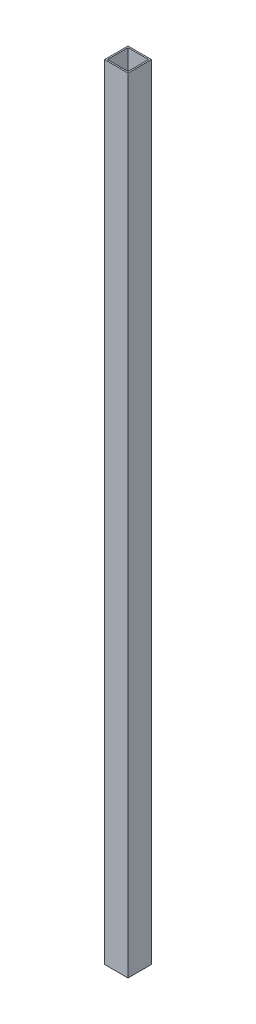
SolidWorks part; units mm, degrees
ref_plane "Front Plane" through (0, 0, 0) normal (0, 0, 1) x (1, 0, 0)
ref_plane "Top Plane" through (0, 0, 0) normal (0, 1, 0) x (1, 0, 0)
ref_plane "Right Plane" through (0, 0, 0) normal (1, 0, 0) x (0, 0, -1)
sketch "Sketch1" plane through (0, 0, 0) normal (0, 1, 0) x (1, 0, 0)
  line L1 (-14.5551, 17.2663) -> (10.8449, 17.2663)
  line L2 (-14.5551, 17.2663) -> (-14.5551, -8.1337)
  line L3 (-14.5551, -8.1337) -> (10.8449, -8.1337)
  line L4 (10.8449, 17.2663) -> (10.8449, -8.1337)
  line L5 (-13.0311, 15.7423) -> (9.3209, 15.7423)
  line L6 (-13.0311, 15.7423) -> (-13.0311, -6.6097)
  line L7 (-13.0311, -6.6097) -> (9.3209, -6.6097)
  line L8 (9.3209, 15.7423) -> (9.3209, -6.6097)
  point P8 (-1.8551, 17.2663)
  point P9 (-14.5551, 4.5663)
  dimension "D1" = 25.4
  dimension "D2" = 25.4
  dimension "D3" = 1.524
  dimension "D4" = 1.524
  dimension "D5" = 1.524
  dimension "D6" = 1.524
extrude "Boss-Extrude1" add sketch "Sketch1" along normal blind 848.868
